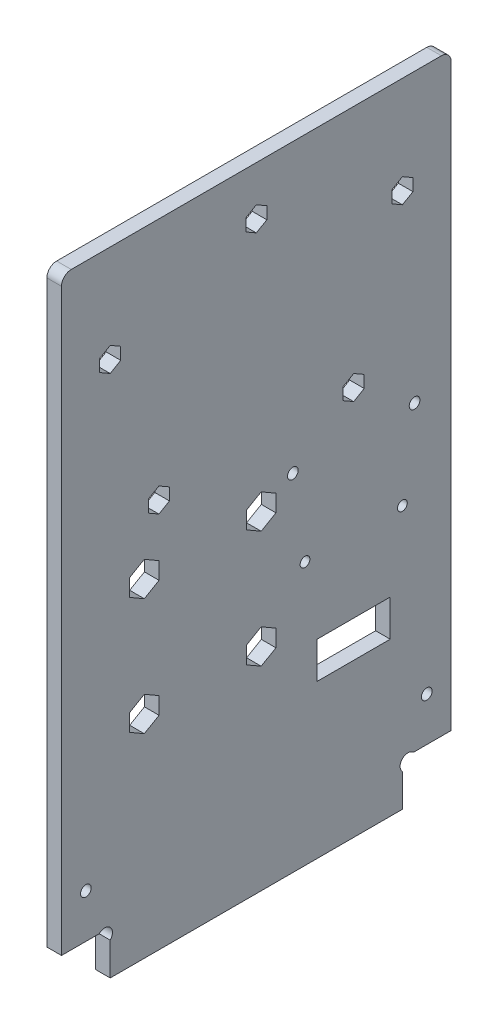
SolidWorks part; units mm, degrees
ref_plane "Plan de face" through (0, 0, 0) normal (0, 0, 1) x (1, 0, 0)
ref_plane "Plan de dessus" through (0, 0, 0) normal (0, 1, 0) x (1, 0, 0)
ref_plane "Plan de droite" through (0, 0, 0) normal (1, 0, 0) x (0, 0, -1)
sketch "Esquisse1" plane through (0, 0, 0) normal (1, 0, 0) x (0, 0, -1)
  line L8 (10, 6.7373) -> (10, 0)
  line L9 (70, 6.7373) -> (70, 0)
  line L10 (7.7373, 9) -> (0, 9)
  line L11 (10, 0) -> (70, 0)
  line L12 (72.2627, 9) -> (80, 9)
  line L13 (0, 9) -> (0, 130)
  line L14 (0, 130) -> (80, 130)
  line L15 (80, 130) -> (80, 9)
  arc A0 (10, 6.7373) -> (7.7373, 9) centre (8.8686, 7.8686) ccw
  arc A1 (70, 6.7373) -> (72.2627, 9) centre (71.1314, 7.8686) cw
  dimension "D7" = 1.1314
  dimension "D6" = 1.6
  dimension "D1" = 9
  dimension "D2" = 10
  dimension "D3" = 10
  dimension "D4" = 80
  dimension "D5" = 130
  dimension "D8" = 1.1314
  dimension "D9" = 1.1314
  dimension "D10" = 1.1314
extrude "Extrusion1" add sketch "Esquisse1" along normal blind 3
sketch "Esquisse2" plane through (3, 0, 0) normal (1, 0, 0) x (0, 0, -1)
  line L0 (0, 9) -> (7.7373, 9) construction
  line L1 (0, 130) -> (0, 9) construction
  line L2 (80, 9) -> (80, 130) construction
  line L3 (72.2627, 9) -> (80, 9) construction
  line L4 (80, 130) -> (0, 130) construction
  circle A0 centre (60, 80) radius 1
  circle A1 centre (10, 110) radius 1
  circle A2 centre (20, 80) radius 1
  circle A3 centre (70, 110) radius 1
  circle A4 centre (17, 67.45) radius 1.5
  circle A5 centre (17, 43.45) radius 1.5
  circle A6 centre (41, 43.45) radius 1.5
  circle A7 centre (41, 67.45) radius 1.5
  circle A8 centre (40, 120) radius 1
  circle A9 centre (70, 54) radius 1
  circle A10 centre (50, 54) radius 1
  dimension "D5" = 17
  dimension "D7" = 10
  dimension "D9" = 10
  dimension "D4" = 3
  dimension "D6" = 2
  dimension "D1" = 58.45
  dimension "D2" = 24
  dimension "D3" = 24
  dimension "D8" = 40
  dimension "D10" = 30
  dimension "D11" = 10
  dimension "D12" = 20
  dimension "D13" = 10
  dimension "D14" = 10
  dimension "D15" = 10
  dimension "D16" = 20
  dimension "D17" = 45
extrude "Enlèv. mat.-Extru.1" cut sketch "Esquisse2" against normal through all
sketch "Esquisse3" plane through (0, 0, 0) normal (-1, 0, 0) x (0, 0, 1)
  line L1 (-67.5, 39) -> (-52.5, 39)
  line L2 (-67.5, 39) -> (-67.5, 31.5)
  line L3 (-67.5, 31.5) -> (-52.5, 31.5)
  line L4 (-52.5, 39) -> (-52.5, 31.5)
  circle A0 centre (-70, 54) radius 1 construction
  circle A1 centre (-50, 54) radius 1 construction
  dimension "D4" = 2.5
  dimension "D1" = 15
  dimension "D2" = 7.5
  dimension "D3" = 15
  dimension "D5" = 2.5
extrude "Enlèv. mat.-Extru.2" cut sketch "Esquisse3" against normal through all
sketch "Esquisse4" plane through (3, 0, 0) normal (1, 0, 0) x (0, 0, -1)
  line L3 (0, 9) -> (7.7373, 9) construction
  line L4 (0, 130) -> (0, 9) construction
  line L5 (80, 9) -> (80, 130) construction
  circle A2 centre (75, 18) radius 1.1
  circle A3 centre (5, 18) radius 1.1
  dimension "D1" = 2.2
  dimension "D2" = 5
  dimension "D3" = 5
  dimension "D5" = 9
extrude "Enlèv. mat.-Extru.3" cut sketch "Esquisse4" against normal through all
sketch "Esquisse5" plane through (3, 0, 0) normal (1, 0, 0) x (0, 0, -1)
  line L0 (0, 130) -> (0, 9) construction
  line L1 (12.1651, 111.25) -> (10, 112.5)
  line L2 (10, 112.5) -> (7.8349, 111.25)
  line L3 (7.8349, 111.25) -> (7.8349, 108.75)
  line L4 (7.8349, 108.75) -> (10, 107.5)
  line L5 (10, 107.5) -> (12.1651, 108.75)
  line L6 (12.1651, 108.75) -> (12.1651, 111.25)
  line L7 (0, 130) -> (0, 9) construction
  line L26 (42.1651, 118.75) -> (42.1651, 121.25)
  line L27 (42.1651, 121.25) -> (40, 122.5)
  line L28 (40, 122.5) -> (37.8349, 121.25)
  line L29 (37.8349, 121.25) -> (37.8349, 118.75)
  line L30 (37.8349, 118.75) -> (40, 117.5)
  line L31 (40, 117.5) -> (42.1651, 118.75)
  line L32 (70, 107.5) -> (72.1651, 108.75)
  line L33 (72.1651, 108.75) -> (72.1651, 111.25)
  line L34 (72.1651, 111.25) -> (70, 112.5)
  line L35 (70, 112.5) -> (67.8349, 111.25)
  line L36 (67.8349, 111.25) -> (67.8349, 108.75)
  line L37 (67.8349, 108.75) -> (70, 107.5)
  line L38 (62.1651, 78.75) -> (62.1651, 81.25)
  line L39 (62.1651, 81.25) -> (60, 82.5)
  line L40 (60, 82.5) -> (57.8349, 81.25)
  line L41 (57.8349, 81.25) -> (57.8349, 78.75)
  line L42 (57.8349, 78.75) -> (60, 77.5)
  line L43 (60, 77.5) -> (62.1651, 78.75)
  line L44 (22.1651, 78.75) -> (22.1651, 81.25)
  line L45 (22.1651, 81.25) -> (20, 82.5)
  line L46 (20, 82.5) -> (17.8349, 81.25)
  line L47 (17.8349, 81.25) -> (17.8349, 78.75)
  line L48 (17.8349, 78.75) -> (20, 77.5)
  line L49 (20, 77.5) -> (22.1651, 78.75)
  line L56 (44.0311, 65.7) -> (44.0311, 69.2)
  line L57 (44.0311, 69.2) -> (41, 70.95)
  line L58 (41, 70.95) -> (37.9689, 69.2)
  line L59 (37.9689, 69.2) -> (37.9689, 65.7)
  line L60 (37.9689, 65.7) -> (41, 63.95)
  line L61 (41, 63.95) -> (44.0311, 65.7)
  line L62 (44.0311, 41.7) -> (44.0311, 45.2)
  line L63 (44.0311, 45.2) -> (41, 46.95)
  line L64 (41, 46.95) -> (37.9689, 45.2)
  line L65 (37.9689, 45.2) -> (37.9689, 41.7)
  line L66 (37.9689, 41.7) -> (41, 39.95)
  line L67 (41, 39.95) -> (44.0311, 41.7)
  line L68 (20.0311, 41.7) -> (20.0311, 45.2)
  line L69 (20.0311, 45.2) -> (17, 46.95)
  line L70 (17, 46.95) -> (13.9689, 45.2)
  line L71 (13.9689, 45.2) -> (13.9689, 41.7)
  line L72 (13.9689, 41.7) -> (17, 39.95)
  line L73 (17, 39.95) -> (20.0311, 41.7)
  line L75 (20.0311, 65.7) -> (20.0311, 69.2)
  line L76 (20.0311, 69.2) -> (17, 70.95)
  line L77 (17, 70.95) -> (13.9689, 69.2)
  line L78 (13.9689, 69.2) -> (13.9689, 65.7)
  line L79 (13.9689, 65.7) -> (17, 63.95)
  line L80 (17, 63.95) -> (20.0311, 65.7)
  circle A0 centre (10, 110) radius 2.1651 construction
  circle A1 centre (40, 120) radius 2.1651 construction
  circle A2 centre (70, 110) radius 2.1651 construction
  circle A3 centre (60, 80) radius 2.1651 construction
  circle A4 centre (20, 80) radius 2.1651 construction
  circle A5 centre (17, 67.45) radius 3.0311 construction
  circle A6 centre (41, 67.45) radius 3.0311 construction
  circle A7 centre (41, 43.45) radius 3.0311 construction
  circle A8 centre (17, 43.45) radius 3.0311 construction
  dimension "D1" = 2.5
  dimension "D2" = 2.5
  dimension "D3" = 2.5
  dimension "D4" = 2.5
  dimension "D5" = 2.5
  dimension "D6" = 3.5
  dimension "D7" = 3.5
  dimension "D8" = 3.5
  dimension "D9" = 3.5
extrude "Enlèv. mat.-Extru.4" cut sketch "Esquisse5" against normal through all
fillet "Congé1" radius 2 2 edges at (1.5, 130, -80) (1.5, 130, 0)
sketch "Esquisse6" plane through (0, 0, 0) normal (-1, 0, 0) x (0, 0, 1)
  line L1 (-67.5, 39) -> (-67.5, 31.5) construction
  line L2 (-52.5, 31.5) -> (-52.5, 39) construction
  circle A0 centre (-72.5, 71) radius 1.1
  circle A1 centre (-47.5, 71) radius 1.1
  circle A2 centre (-70, 54) radius 1 construction
  dimension "D1" = 2.2
  dimension "D2" = 2.2
  dimension "D3" = 17
  dimension "D4" = 5
  dimension "D5" = 5
extrude "Enlèv. mat.-Extru.5" cut sketch "Esquisse6" against normal through all
